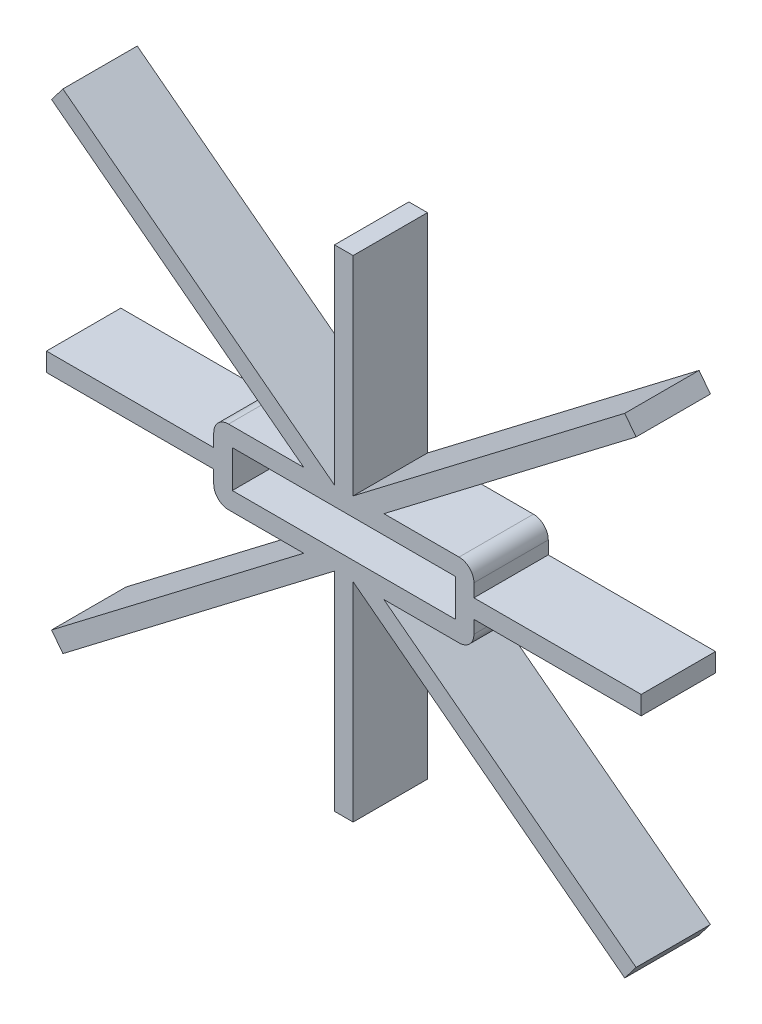
SolidWorks part; units mm, degrees
ref_plane "Front Plane" through (0, 0, 0) normal (0, 0, 1) x (1, 0, 0)
ref_plane "Top Plane" through (0, 0, 0) normal (0, 1, 0) x (1, 0, 0)
ref_plane "Right Plane" through (0, 0, 0) normal (1, 0, 0) x (0, 0, -1)
sketch "Sketch1" plane through (0, 0, 0) normal (0, 0, 1) x (1, 0, 0)
  line L0 (0, -83.82) -> (0, 83.82) construction
  line L1 (-38.1, 6.35) -> (38.1, 6.35)
  line L2 (-38.1, 6.35) -> (-38.1, -6.35)
  line L3 (-38.1, -6.35) -> (38.1, -6.35)
  line L4 (38.1, 6.35) -> (38.1, -6.35)
  line L5 (-38.1, 6.35) -> (38.1, -6.35) construction
  line L6 (-38.1, -6.35) -> (38.1, 6.35) construction
  line L7 (44.45, 12.7) -> (-44.45, 12.7)
  line L8 (44.45, 12.7) -> (44.45, -12.7)
  line L9 (44.45, -12.7) -> (-44.45, -12.7)
  line L10 (-44.45, 12.7) -> (-44.45, -12.7)
  line L11 (44.45, 12.7) -> (-44.45, -12.7) construction
  line L12 (44.45, -12.7) -> (-44.45, 12.7) construction
  line L13 (3.175, 83.82) -> (-3.175, 83.82)
  line L14 (-3.175, 83.82) -> (-3.175, 12.7)
  line L15 (101.6, 0) -> (-101.6, 0) construction
  line L16 (-101.6, -3.175) -> (-101.6, 3.175)
  line L17 (-101.6, 3.175) -> (-44.45, 3.175)
  line L18 (-8.4328, 12.7) -> (-101.6, 83.82) construction
  line L19 (-3.175, 12.7) -> (-95.9837, 83.5463)
  line L20 (-95.9837, 83.5463) -> (-97.9195, 81.0104)
  line L21 (-13.6906, 12.7) -> (-99.8552, 78.4745)
  line L22 (-99.8552, 78.4745) -> (-97.9195, 81.0104)
  line L23 (3.175, 83.82) -> (3.175, 12.7)
  line L24 (95.9837, 83.5463) -> (97.9195, 81.0104)
  line L25 (99.8552, 78.4745) -> (97.9195, 81.0104)
  line L26 (3.175, 12.7) -> (95.9837, 83.5463)
  line L27 (8.4328, 12.7) -> (101.6, 83.82) construction
  line L28 (13.6906, 12.7) -> (99.8552, 78.4745)
  line L29 (99.8552, -78.4745) -> (97.9195, -81.0104)
  line L30 (95.9837, -83.5463) -> (97.9195, -81.0104)
  line L31 (13.6906, -12.7) -> (99.8552, -78.4745)
  line L32 (8.4328, -12.7) -> (101.6, -83.82) construction
  line L33 (3.175, -12.7) -> (95.9837, -83.5463)
  line L34 (3.175, -83.82) -> (-3.175, -83.82)
  line L35 (3.175, -83.82) -> (3.175, -12.7)
  line L36 (-3.175, -83.82) -> (-3.175, -12.7)
  line L37 (-99.8552, -78.4745) -> (-97.9195, -81.0104)
  line L38 (-95.9837, -83.5463) -> (-97.9195, -81.0104)
  line L39 (-3.175, -12.7) -> (-95.9837, -83.5463)
  line L40 (-8.4328, -12.7) -> (-101.6, -83.82) construction
  line L41 (-13.6906, -12.7) -> (-99.8552, -78.4745)
  line L42 (-101.6, -3.175) -> (-44.45, -3.175)
  line L43 (101.6, 3.175) -> (44.45, 3.175)
  line L44 (101.6, -3.175) -> (101.6, 3.175)
  line L45 (101.6, -3.175) -> (44.45, -3.175)
  point P0 (0, 0)
  point P6 (0, 0)
  point P52 (0, 0)
  dimension "D1" = 76.2
  dimension "D2" = 12.7
  dimension "D3" = 6.35
  dimension "D4" = 6.35
  dimension "D5" = 83.82
  dimension "D6" = 3.175
  dimension "D7" = 101.6
  dimension "D8" = 3.175
  dimension "D9" = 5.2578
  dimension "D10" = 5.2578
  dimension "D11" = 6.3806
extrude "Boss-Extrude1" add sketch "Sketch1" along normal blind 25.4 contours L7 L10 L9 L8 L1 L4 L3 L2 | L45 L44 L43 L8 | L9 L33 L30 L29 L31 | L36 L34 L35 L9 | L9 L41 L37 L38 L39 | L16 L42 L10 L17 | L22 L21 L7 L19 L20 | L23 L13 L14 L7 | L7 L28 L25 L24 L26
fillet "Fillet1" radius 5.08 4 edges at (-44.45, 12.7, 12.7) (-44.45, -12.7, 12.7) (44.45, -12.7, 12.7) (44.45, 12.7, 12.7)
